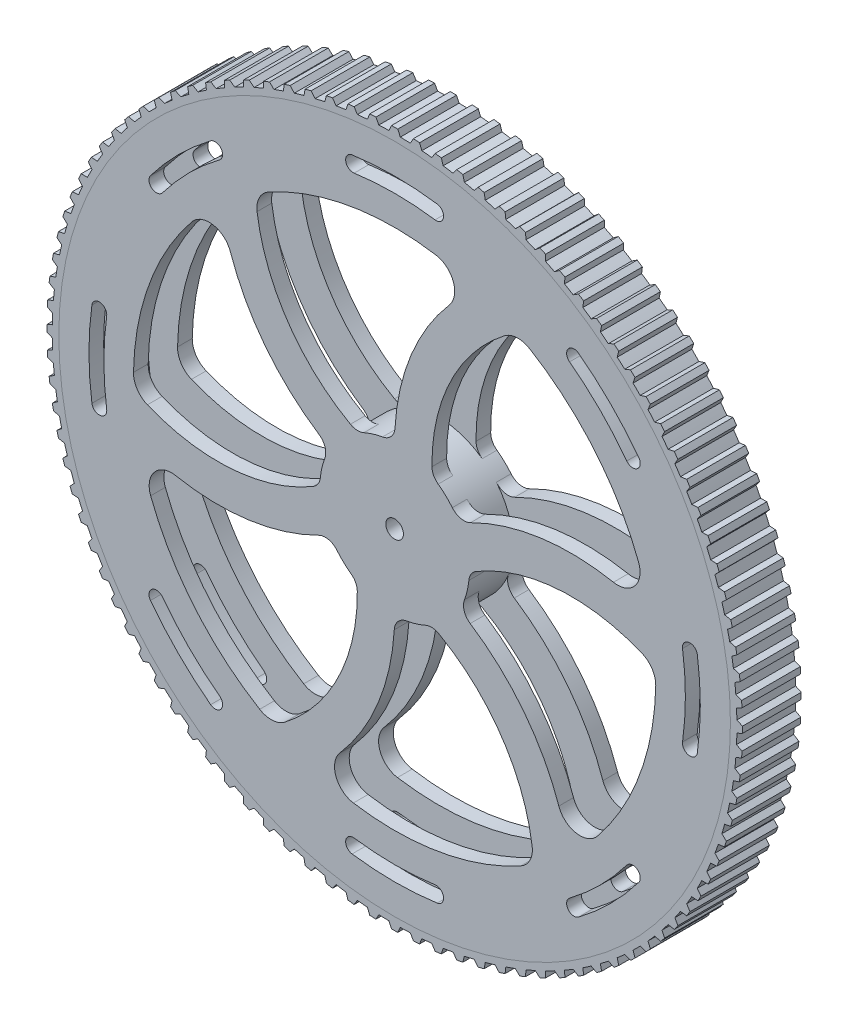
SolidWorks part; units mm, degrees
material "Acrylic (Medium-high impact)"
ref_plane "Front Plane" through (0, 0, 0) normal (0, 0, 1) x (1, 0, 0)
ref_plane "Top Plane" through (0, 0, 0) normal (0, 1, 0) x (1, 0, 0)
ref_plane "Right Plane" through (0, 0, 0) normal (1, 0, 0) x (0, 0, -1)
sketch "Sketch1" plane through (0, 0, 0) normal (0, 0, 1) x (1, 0, 0)
  circle A0 centre (0, 0) radius 114.3
  dimension "D1" = 228.6
extrude "Boss-Extrude1" add sketch "Sketch1" along normal mid plane 20
sketch "Sketch3" plane through (0, 0, 0) normal (0, 0, 1) x (1, 0, 0)
  line L0 (0, 0) -> (0, 114.3) construction
  circle A0 centre (0, 0) radius 114.3 construction
  circle A1 centre (0, 0) radius 88.9
  circle A2 centre (0, 0) radius 25.4
  arc A3 (27.9624, 84.3879) -> (0, 25.4) centre (76.2, 25.4) ccw
  arc A4 (41.5327, 78.6018) -> (12.7942, 21.9424) centre (76.2, 25.4) ccw
  arc A5 (87.0632, 17.9778) -> (21.997, 12.7) centre (60.097, -53.2911) ccw
  arc A6 (34.5993, 89.2422) -> (0.113, 21.2509) centre (76.2, 25.4) ccw construction
  arc A7 (88.8375, 3.3325) -> (25.3998, -0.1089) centre (60.097, -53.2911) ccw
  arc A8 (59.1009, -66.4101) -> (21.997, -12.7) centre (-16.103, -78.6911) ccw
  arc A9 (47.3048, -75.2693) -> (12.6056, -22.0513) centre (-16.103, -78.6911) ccw
  arc A10 (-27.9624, -84.3879) -> (0, -25.4) centre (-76.2, -25.4) ccw
  arc A11 (-41.5327, -78.6018) -> (-12.7942, -21.9424) centre (-76.2, -25.4) ccw
  arc A12 (-87.0632, -17.9778) -> (-21.997, -12.7) centre (-60.097, 53.2911) ccw
  arc A13 (-88.8375, -3.3325) -> (-25.3998, 0.1089) centre (-60.097, 53.2911) ccw
  arc A14 (-59.1009, 66.4101) -> (-21.997, 12.7) centre (16.103, 78.6911) ccw
  arc A15 (-47.3048, 75.2693) -> (-12.6056, 22.0513) centre (16.103, 78.6911) ccw
  point P50 (0, 0)
  dimension "D1" = 177.8
  dimension "D2" = 50.8
  dimension "D3" = 63.5
  dimension "D4" = 25.4
  dimension "D5" = 76.2
  dimension "D7" = 27.9624
  dimension "D8" = 84.3879
  dimension "D6" = 12.7
extrude "Cut-Extrude1" cut sketch "Sketch3" against normal mid plane 127 contours A14 A1 A13 A2 | A1 A15 A2 A3 | A5 A1 A4 A2 | A8 A1 A7 A2 | A10 A1 A9 A2 | A12 A1 A11 A2
fillet "Fillet1" radius 7.62 12 edges at (88.8375, 3.3325, 0) (59.1009, -66.4101, 0) (47.3048, -75.2693, 0) (-27.9624, -84.3879, 0) (-41.5327, -78.6018, 0) (-87.0632, -17.9778, 0) (87.0632, 17.9778, 0) (41.5327, 78.6018, 0) (27.9624, 84.3879, 0) (-47.3048, 75.2693, 0) (-59.1009, 66.4101, 0) (-88.8375, -3.3325, 0)
fillet "Fillet2" radius 5.08 12 edges at (-25.3998, 0.1089, 0) (-21.997, 12.7, 0) (0, 25.4, 0) (-12.6056, 22.0513, 0) (12.7942, 21.9424, 0) (21.997, 12.7, 0) (25.3998, -0.1089, 0) (21.997, -12.7, 0) (12.6056, -22.0513, 0) (0, -25.4, 0) (-12.7942, -21.9424, 0) (-21.997, -12.7, 0)
sketch "Sketch4" plane through (0, 0, 10) normal (0, 0, 1) x (1, 0, 0)
  circle A0 centre (0, 0) radius 3
  dimension "D1" = 6
extrude "Cut-Extrude2" cut sketch "Sketch4" against normal blind 127
sketch "Sketch5" plane through (0, 0, 0) normal (0, 0, 1) x (1, 0, 0)
  line L0 (0, 2.0217) -> (0, 118.4) construction
  line L1 (0, 2.0217) -> (0, 116.4837) construction
  line L2 (-1.0586, 118.3953) -> (-1.95, 116.4837)
  line L3 (1.0586, 118.3953) -> (1.95, 116.4837)
  line L4 (-1.95, 116.4837) -> (1.95, 116.4837) construction
  line L5 (8.4906, 118.0952) -> (9.2602, 116.1314)
  line L6 (6.3776, 118.2281) -> (5.3679, 116.3763)
  line L7 (15.8891, 117.329) -> (16.5339, 115.3208)
  line L8 (13.7886, 117.5944) -> (12.6647, 115.8096)
  line L9 (23.2249, 116.0998) -> (23.7423, 114.055)
  line L10 (21.1452, 116.4965) -> (19.9114, 114.7858)
  line L11 (30.4691, 114.4124) -> (30.8571, 112.3392)
  line L12 (28.4184, 114.9389) -> (27.0796, 113.3091)
  line L13 (37.5929, 112.2735) -> (37.85, 110.18)
  line L14 (35.5794, 112.9277) -> (34.1409, 111.3851)
  line L15 (44.5685, 109.6914) -> (44.6936, 107.5859)
  line L16 (42.5999, 110.4708) -> (41.0674, 109.0216)
  line L17 (51.3681, 106.6765) -> (51.3608, 104.5673)
  line L18 (49.4524, 107.578) -> (47.8319, 106.2279)
  line L19 (57.965, 103.2406) -> (57.8252, 101.136)
  line L20 (56.1097, 104.2606) -> (54.4076, 103.0148)
  line L21 (64.3332, 99.3972) -> (64.0615, 97.3056)
  line L22 (62.5455, 100.5317) -> (60.7686, 99.3953)
  line L23 (70.4474, 95.1615) -> (70.045, 93.0911)
  line L24 (68.7346, 96.406) -> (66.8898, 95.3835)
  line L25 (76.2837, 90.5503) -> (75.752, 88.5092)
  line L26 (74.6523, 91.8999) -> (72.747, 90.9952)
  line L27 (81.8188, 85.5818) -> (81.1601, 83.5781)
  line L28 (80.2754, 87.0311) -> (78.3171, 86.2478)
  line L29 (87.0311, 80.2754) -> (86.2478, 78.3171)
  line L30 (85.5818, 81.8188) -> (83.5781, 81.1601)
  line L31 (91.8999, 74.6523) -> (90.9952, 72.747)
  line L32 (90.5503, 76.2837) -> (88.5092, 75.752)
  line L33 (96.406, 68.7346) -> (95.3835, 66.8898)
  line L34 (95.1615, 70.4474) -> (93.0911, 70.045)
  line L35 (100.5317, 62.5455) -> (99.3953, 60.7686)
  line L36 (99.3972, 64.3332) -> (97.3056, 64.0615)
  line L37 (104.2606, 56.1097) -> (103.0148, 54.4076)
  line L38 (103.2406, 57.965) -> (101.136, 57.8252)
  line L39 (107.578, 49.4524) -> (106.2279, 47.8319)
  line L40 (106.6765, 51.3681) -> (104.5673, 51.3608)
  line L41 (110.4708, 42.5999) -> (109.0216, 41.0674)
  line L42 (109.6914, 44.5685) -> (107.5859, 44.6936)
  line L43 (112.9277, 35.5794) -> (111.3851, 34.1409)
  line L44 (112.2735, 37.5929) -> (110.18, 37.85)
  line L45 (114.9389, 28.4184) -> (113.3091, 27.0796)
  line L46 (114.4124, 30.4691) -> (112.3392, 30.8571)
  line L47 (116.4965, 21.1452) -> (114.7858, 19.9114)
  line L48 (116.0998, 23.2249) -> (114.055, 23.7423)
  line L49 (117.5944, 13.7886) -> (115.8096, 12.6647)
  line L50 (117.329, 15.8891) -> (115.3208, 16.5339)
  line L51 (118.2281, 6.3776) -> (116.3763, 5.3679)
  line L52 (118.0952, 8.4906) -> (116.1314, 9.2602)
  line L53 (118.3953, -1.0586) -> (116.4837, -1.95)
  line L54 (118.3953, 1.0586) -> (116.4837, 1.95)
  line L55 (118.0952, -8.4906) -> (116.1314, -9.2602)
  line L56 (118.2281, -6.3776) -> (116.3763, -5.3679)
  line L57 (117.329, -15.8891) -> (115.3208, -16.5339)
  line L58 (117.5944, -13.7886) -> (115.8096, -12.6647)
  line L59 (116.0998, -23.2249) -> (114.055, -23.7423)
  line L60 (116.4965, -21.1452) -> (114.7858, -19.9114)
  line L61 (114.4124, -30.4691) -> (112.3392, -30.8571)
  line L62 (114.9389, -28.4184) -> (113.3091, -27.0796)
  line L63 (112.2735, -37.5929) -> (110.18, -37.85)
  line L64 (112.9277, -35.5794) -> (111.3851, -34.1409)
  line L65 (109.6914, -44.5685) -> (107.5859, -44.6936)
  line L66 (110.4708, -42.5999) -> (109.0216, -41.0674)
  line L67 (106.6765, -51.3681) -> (104.5673, -51.3608)
  line L68 (107.578, -49.4524) -> (106.2279, -47.8319)
  line L69 (103.2406, -57.965) -> (101.136, -57.8252)
  line L70 (104.2606, -56.1097) -> (103.0148, -54.4076)
  line L71 (99.3972, -64.3332) -> (97.3056, -64.0615)
  line L72 (100.5317, -62.5455) -> (99.3953, -60.7686)
  line L73 (95.1615, -70.4474) -> (93.0911, -70.045)
  line L74 (96.406, -68.7346) -> (95.3835, -66.8898)
  line L75 (90.5503, -76.2837) -> (88.5092, -75.752)
  line L76 (91.8999, -74.6523) -> (90.9952, -72.747)
  line L77 (85.5818, -81.8188) -> (83.5781, -81.1601)
  line L78 (87.0311, -80.2754) -> (86.2478, -78.3171)
  line L79 (80.2754, -87.0311) -> (78.3171, -86.2478)
  line L80 (81.8188, -85.5818) -> (81.1601, -83.5781)
  line L81 (74.6523, -91.8999) -> (72.747, -90.9952)
  line L82 (76.2837, -90.5503) -> (75.752, -88.5092)
  line L83 (68.7346, -96.406) -> (66.8898, -95.3835)
  line L84 (70.4474, -95.1615) -> (70.045, -93.0911)
  line L85 (62.5455, -100.5317) -> (60.7686, -99.3953)
  line L86 (64.3332, -99.3972) -> (64.0615, -97.3056)
  line L87 (56.1097, -104.2606) -> (54.4076, -103.0148)
  line L88 (57.965, -103.2406) -> (57.8252, -101.136)
  line L89 (49.4524, -107.578) -> (47.8319, -106.2279)
  line L90 (51.3681, -106.6765) -> (51.3608, -104.5673)
  line L91 (42.5999, -110.4708) -> (41.0674, -109.0216)
  line L92 (44.5685, -109.6914) -> (44.6936, -107.5859)
  line L93 (35.5794, -112.9277) -> (34.1409, -111.3851)
  line L94 (37.5929, -112.2735) -> (37.85, -110.18)
  line L95 (28.4184, -114.9389) -> (27.0796, -113.3091)
  line L96 (30.4691, -114.4124) -> (30.8571, -112.3392)
  line L97 (21.1452, -116.4965) -> (19.9114, -114.7858)
  line L98 (23.2249, -116.0998) -> (23.7423, -114.055)
  line L99 (13.7886, -117.5944) -> (12.6647, -115.8096)
  line L100 (15.8891, -117.329) -> (16.5339, -115.3208)
  line L101 (6.3776, -118.2281) -> (5.3679, -116.3763)
  line L102 (8.4906, -118.0952) -> (9.2602, -116.1314)
  line L103 (-1.0586, -118.3953) -> (-1.95, -116.4837)
  line L104 (1.0586, -118.3953) -> (1.95, -116.4837)
  line L105 (-8.4906, -118.0952) -> (-9.2602, -116.1314)
  line L106 (-6.3776, -118.2281) -> (-5.3679, -116.3763)
  line L107 (-15.8891, -117.329) -> (-16.5339, -115.3208)
  line L108 (-13.7886, -117.5944) -> (-12.6647, -115.8096)
  line L109 (-23.2249, -116.0998) -> (-23.7423, -114.055)
  line L110 (-21.1452, -116.4965) -> (-19.9114, -114.7858)
  line L111 (-30.4691, -114.4124) -> (-30.8571, -112.3392)
  line L112 (-28.4184, -114.9389) -> (-27.0796, -113.3091)
  line L113 (-37.5929, -112.2735) -> (-37.85, -110.18)
  line L114 (-35.5794, -112.9277) -> (-34.1409, -111.3851)
  line L115 (-44.5685, -109.6914) -> (-44.6936, -107.5859)
  line L116 (-42.5999, -110.4708) -> (-41.0674, -109.0216)
  line L117 (-51.3681, -106.6765) -> (-51.3608, -104.5673)
  line L118 (-49.4524, -107.578) -> (-47.8319, -106.2279)
  line L119 (-57.965, -103.2406) -> (-57.8252, -101.136)
  line L120 (-56.1097, -104.2606) -> (-54.4076, -103.0148)
  line L121 (-64.3332, -99.3972) -> (-64.0615, -97.3056)
  line L122 (-62.5455, -100.5317) -> (-60.7686, -99.3953)
  line L123 (-70.4474, -95.1615) -> (-70.045, -93.0911)
  line L124 (-68.7346, -96.406) -> (-66.8898, -95.3835)
  line L125 (-76.2837, -90.5503) -> (-75.752, -88.5092)
  line L126 (-74.6523, -91.8999) -> (-72.747, -90.9952)
  line L127 (-81.8188, -85.5818) -> (-81.1601, -83.5781)
  line L128 (-80.2754, -87.0311) -> (-78.3171, -86.2478)
  line L129 (-87.0311, -80.2754) -> (-86.2478, -78.3171)
  line L130 (-85.5818, -81.8188) -> (-83.5781, -81.1601)
  line L131 (-91.8999, -74.6523) -> (-90.9952, -72.747)
  line L132 (-90.5503, -76.2837) -> (-88.5092, -75.752)
  line L133 (-96.406, -68.7346) -> (-95.3835, -66.8898)
  line L134 (-95.1615, -70.4474) -> (-93.0911, -70.045)
  line L135 (-100.5317, -62.5455) -> (-99.3953, -60.7686)
  line L136 (-99.3972, -64.3332) -> (-97.3056, -64.0615)
  line L137 (-104.2606, -56.1097) -> (-103.0148, -54.4076)
  line L138 (-103.2406, -57.965) -> (-101.136, -57.8252)
  line L139 (-107.578, -49.4524) -> (-106.2279, -47.8319)
  line L140 (-106.6765, -51.3681) -> (-104.5673, -51.3608)
  line L141 (-110.4708, -42.5999) -> (-109.0216, -41.0674)
  line L142 (-109.6914, -44.5685) -> (-107.5859, -44.6936)
  line L143 (-112.9277, -35.5794) -> (-111.3851, -34.1409)
  line L144 (-112.2735, -37.5929) -> (-110.18, -37.85)
  line L145 (-114.9389, -28.4184) -> (-113.3091, -27.0796)
  line L146 (-114.4124, -30.4691) -> (-112.3392, -30.8571)
  line L147 (-116.4965, -21.1452) -> (-114.7858, -19.9114)
  line L148 (-116.0998, -23.2249) -> (-114.055, -23.7423)
  line L149 (-117.5944, -13.7886) -> (-115.8096, -12.6647)
  line L150 (-117.329, -15.8891) -> (-115.3208, -16.5339)
  line L151 (-118.2281, -6.3776) -> (-116.3763, -5.3679)
  line L152 (-118.0952, -8.4906) -> (-116.1314, -9.2602)
  line L153 (-118.3953, 1.0586) -> (-116.4837, 1.95)
  line L154 (-118.3953, -1.0586) -> (-116.4837, -1.95)
  line L155 (-118.0952, 8.4906) -> (-116.1314, 9.2602)
  line L156 (-118.2281, 6.3776) -> (-116.3763, 5.3679)
  line L157 (-117.329, 15.8891) -> (-115.3208, 16.5339)
  line L158 (-117.5944, 13.7886) -> (-115.8096, 12.6647)
  line L159 (-116.0998, 23.2249) -> (-114.055, 23.7423)
  line L160 (-116.4965, 21.1452) -> (-114.7858, 19.9114)
  line L161 (-114.4124, 30.4691) -> (-112.3392, 30.8571)
  line L162 (-114.9389, 28.4184) -> (-113.3091, 27.0796)
  line L163 (-112.2735, 37.5929) -> (-110.18, 37.85)
  line L164 (-112.9277, 35.5794) -> (-111.3851, 34.1409)
  line L165 (-109.6914, 44.5685) -> (-107.5859, 44.6936)
  line L166 (-110.4708, 42.5999) -> (-109.0216, 41.0674)
  line L167 (-106.6765, 51.3681) -> (-104.5673, 51.3608)
  line L168 (-107.578, 49.4524) -> (-106.2279, 47.8319)
  line L169 (-103.2406, 57.965) -> (-101.136, 57.8252)
  line L170 (-104.2606, 56.1097) -> (-103.0148, 54.4076)
  line L171 (-99.3972, 64.3332) -> (-97.3056, 64.0615)
  line L172 (-100.5317, 62.5455) -> (-99.3953, 60.7686)
  line L173 (-95.1615, 70.4474) -> (-93.0911, 70.045)
  line L174 (-96.406, 68.7346) -> (-95.3835, 66.8898)
  line L175 (-90.5503, 76.2837) -> (-88.5092, 75.752)
  line L176 (-91.8999, 74.6523) -> (-90.9952, 72.747)
  line L177 (-85.5818, 81.8188) -> (-83.5781, 81.1601)
  line L178 (-87.0311, 80.2754) -> (-86.2478, 78.3171)
  line L179 (-80.2754, 87.0311) -> (-78.3171, 86.2478)
  line L180 (-81.8188, 85.5818) -> (-81.1601, 83.5781)
  line L181 (-74.6523, 91.8999) -> (-72.747, 90.9952)
  line L182 (-76.2837, 90.5503) -> (-75.752, 88.5092)
  line L183 (-68.7346, 96.406) -> (-66.8898, 95.3835)
  line L184 (-70.4474, 95.1615) -> (-70.045, 93.0911)
  line L185 (-62.5455, 100.5317) -> (-60.7686, 99.3953)
  line L186 (-64.3332, 99.3972) -> (-64.0615, 97.3056)
  line L187 (-56.1097, 104.2606) -> (-54.4076, 103.0148)
  line L188 (-57.965, 103.2406) -> (-57.8252, 101.136)
  line L189 (-49.4524, 107.578) -> (-47.8319, 106.2279)
  line L190 (-51.3681, 106.6765) -> (-51.3608, 104.5673)
  line L191 (-42.5999, 110.4708) -> (-41.0674, 109.0216)
  line L192 (-44.5685, 109.6914) -> (-44.6936, 107.5859)
  line L193 (-35.5794, 112.9277) -> (-34.1409, 111.3851)
  line L194 (-37.5929, 112.2735) -> (-37.85, 110.18)
  line L195 (-28.4184, 114.9389) -> (-27.0796, 113.3091)
  line L196 (-30.4691, 114.4124) -> (-30.8571, 112.3392)
  line L197 (-21.1452, 116.4965) -> (-19.9114, 114.7858)
  line L198 (-23.2249, 116.0998) -> (-23.7423, 114.055)
  line L199 (-13.7886, 117.5944) -> (-12.6647, 115.8096)
  line L200 (-15.8891, 117.329) -> (-16.5339, 115.3208)
  line L201 (-6.3776, 118.2281) -> (-5.3679, 116.3763)
  line L202 (-8.4906, 118.0952) -> (-9.2602, 116.1314)
  circle A0 centre (0, 0) radius 114.3 construction
  circle A1 centre (0, 0) radius 114.3
  arc A2 (1.0586, 118.3953) -> (-1.0586, 118.3953) centre (0, 0) ccw
  arc A3 (5.3679, 116.3763) -> (1.95, 116.4837) centre (0, 0) ccw
  arc A4 (8.4906, 118.0952) -> (6.3776, 118.2281) centre (0, 0) ccw
  circle A5 centre (0, 0) radius 118.4 construction
  arc A6 (15.8891, 117.329) -> (13.7886, 117.5944) centre (0, 0) ccw
  arc A7 (23.2249, 116.0998) -> (21.1452, 116.4965) centre (0, 0) ccw
  arc A8 (30.4691, 114.4124) -> (28.4184, 114.9389) centre (0, 0) ccw
  arc A9 (37.5929, 112.2735) -> (35.5794, 112.9277) centre (0, 0) ccw
  arc A10 (44.5685, 109.6914) -> (42.5999, 110.4708) centre (0, 0) ccw
  arc A11 (51.3681, 106.6765) -> (49.4524, 107.578) centre (0, 0) ccw
  arc A12 (57.965, 103.2406) -> (56.1097, 104.2606) centre (0, 0) ccw
  arc A13 (64.3332, 99.3972) -> (62.5455, 100.5317) centre (0, 0) ccw
  arc A14 (70.4474, 95.1615) -> (68.7346, 96.406) centre (0, 0) ccw
  arc A15 (76.2837, 90.5503) -> (74.6523, 91.8999) centre (0, 0) ccw
  arc A16 (81.8188, 85.5818) -> (80.2754, 87.0311) centre (0, 0) ccw
  arc A17 (87.0311, 80.2754) -> (85.5818, 81.8188) centre (0, 0) ccw
  arc A18 (91.8999, 74.6523) -> (90.5503, 76.2837) centre (0, 0) ccw
  arc A19 (96.406, 68.7346) -> (95.1615, 70.4474) centre (0, 0) ccw
  arc A20 (100.5317, 62.5455) -> (99.3972, 64.3332) centre (0, 0) ccw
  arc A21 (104.2606, 56.1097) -> (103.2406, 57.965) centre (0, 0) ccw
  arc A22 (107.578, 49.4524) -> (106.6765, 51.3681) centre (0, 0) ccw
  arc A23 (110.4708, 42.5999) -> (109.6914, 44.5685) centre (0, 0) ccw
  arc A24 (112.9277, 35.5794) -> (112.2735, 37.5929) centre (0, 0) ccw
  arc A25 (114.9389, 28.4184) -> (114.4124, 30.4691) centre (0, 0) ccw
  arc A26 (116.4965, 21.1452) -> (116.0998, 23.2249) centre (0, 0) ccw
  arc A27 (117.5944, 13.7886) -> (117.329, 15.8891) centre (0, 0) ccw
  arc A28 (118.2281, 6.3776) -> (118.0952, 8.4906) centre (0, 0) ccw
  arc A29 (118.3953, -1.0586) -> (118.3953, 1.0586) centre (0, 0) ccw
  arc A30 (118.0952, -8.4906) -> (118.2281, -6.3776) centre (0, 0) ccw
  arc A31 (117.329, -15.8891) -> (117.5944, -13.7886) centre (0, 0) ccw
  arc A32 (116.0998, -23.2249) -> (116.4965, -21.1452) centre (0, 0) ccw
  arc A33 (114.4124, -30.4691) -> (114.9389, -28.4184) centre (0, 0) ccw
  arc A34 (112.2735, -37.5929) -> (112.9277, -35.5794) centre (0, 0) ccw
  arc A35 (109.6914, -44.5685) -> (110.4708, -42.5999) centre (0, 0) ccw
  arc A36 (106.6765, -51.3681) -> (107.578, -49.4524) centre (0, 0) ccw
  arc A37 (103.2406, -57.965) -> (104.2606, -56.1097) centre (0, 0) ccw
  arc A38 (99.3972, -64.3332) -> (100.5317, -62.5455) centre (0, 0) ccw
  arc A39 (95.1615, -70.4474) -> (96.406, -68.7346) centre (0, 0) ccw
  arc A40 (90.5503, -76.2837) -> (91.8999, -74.6523) centre (0, 0) ccw
  arc A41 (85.5818, -81.8188) -> (87.0311, -80.2754) centre (0, 0) ccw
  arc A42 (80.2754, -87.0311) -> (81.8188, -85.5818) centre (0, 0) ccw
  arc A43 (74.6523, -91.8999) -> (76.2837, -90.5503) centre (0, 0) ccw
  arc A44 (68.7346, -96.406) -> (70.4474, -95.1615) centre (0, 0) ccw
  arc A45 (62.5455, -100.5317) -> (64.3332, -99.3972) centre (0, 0) ccw
  arc A46 (56.1097, -104.2606) -> (57.965, -103.2406) centre (0, 0) ccw
  arc A47 (49.4524, -107.578) -> (51.3681, -106.6765) centre (0, 0) ccw
  arc A48 (42.5999, -110.4708) -> (44.5685, -109.6914) centre (0, 0) ccw
  arc A49 (35.5794, -112.9277) -> (37.5929, -112.2735) centre (0, 0) ccw
  arc A50 (28.4184, -114.9389) -> (30.4691, -114.4124) centre (0, 0) ccw
  arc A51 (21.1452, -116.4965) -> (23.2249, -116.0998) centre (0, 0) ccw
  arc A52 (13.7886, -117.5944) -> (15.8891, -117.329) centre (0, 0) ccw
  arc A53 (6.3776, -118.2281) -> (8.4906, -118.0952) centre (0, 0) ccw
  arc A54 (-1.0586, -118.3953) -> (1.0586, -118.3953) centre (0, 0) ccw
  arc A55 (-8.4906, -118.0952) -> (-6.3776, -118.2281) centre (0, 0) ccw
  arc A56 (-15.8891, -117.329) -> (-13.7886, -117.5944) centre (0, 0) ccw
  arc A57 (-23.2249, -116.0998) -> (-21.1452, -116.4965) centre (0, 0) ccw
  arc A58 (-30.4691, -114.4124) -> (-28.4184, -114.9389) centre (0, 0) ccw
  arc A59 (-37.5929, -112.2735) -> (-35.5794, -112.9277) centre (0, 0) ccw
  arc A60 (-44.5685, -109.6914) -> (-42.5999, -110.4708) centre (0, 0) ccw
  arc A61 (-51.3681, -106.6765) -> (-49.4524, -107.578) centre (0, 0) ccw
  arc A62 (-57.965, -103.2406) -> (-56.1097, -104.2606) centre (0, 0) ccw
  arc A63 (-64.3332, -99.3972) -> (-62.5455, -100.5317) centre (0, 0) ccw
  arc A64 (-70.4474, -95.1615) -> (-68.7346, -96.406) centre (0, 0) ccw
  arc A65 (-76.2837, -90.5503) -> (-74.6523, -91.8999) centre (0, 0) ccw
  arc A66 (-81.8188, -85.5818) -> (-80.2754, -87.0311) centre (0, 0) ccw
  arc A67 (-87.0311, -80.2754) -> (-85.5818, -81.8188) centre (0, 0) ccw
  arc A68 (-91.8999, -74.6523) -> (-90.5503, -76.2837) centre (0, 0) ccw
  arc A69 (-96.406, -68.7346) -> (-95.1615, -70.4474) centre (0, 0) ccw
  arc A70 (-100.5317, -62.5455) -> (-99.3972, -64.3332) centre (0, 0) ccw
  arc A71 (-104.2606, -56.1097) -> (-103.2406, -57.965) centre (0, 0) ccw
  arc A72 (-107.578, -49.4524) -> (-106.6765, -51.3681) centre (0, 0) ccw
  arc A73 (-110.4708, -42.5999) -> (-109.6914, -44.5685) centre (0, 0) ccw
  arc A74 (-112.9277, -35.5794) -> (-112.2735, -37.5929) centre (0, 0) ccw
  arc A75 (-114.9389, -28.4184) -> (-114.4124, -30.4691) centre (0, 0) ccw
  arc A76 (-116.4965, -21.1452) -> (-116.0998, -23.2249) centre (0, 0) ccw
  arc A77 (-117.5944, -13.7886) -> (-117.329, -15.8891) centre (0, 0) ccw
  arc A78 (-118.2281, -6.3776) -> (-118.0952, -8.4906) centre (0, 0) ccw
  arc A79 (-118.3953, 1.0586) -> (-118.3953, -1.0586) centre (0, 0) ccw
  arc A80 (-118.0952, 8.4906) -> (-118.2281, 6.3776) centre (0, 0) ccw
  arc A81 (-117.329, 15.8891) -> (-117.5944, 13.7886) centre (0, 0) ccw
  arc A82 (-116.0998, 23.2249) -> (-116.4965, 21.1452) centre (0, 0) ccw
  arc A83 (-114.4124, 30.4691) -> (-114.9389, 28.4184) centre (0, 0) ccw
  arc A84 (-112.2735, 37.5929) -> (-112.9277, 35.5794) centre (0, 0) ccw
  arc A85 (-109.6914, 44.5685) -> (-110.4708, 42.5999) centre (0, 0) ccw
  arc A86 (-106.6765, 51.3681) -> (-107.578, 49.4524) centre (0, 0) ccw
  arc A87 (-103.2406, 57.965) -> (-104.2606, 56.1097) centre (0, 0) ccw
  arc A88 (-99.3972, 64.3332) -> (-100.5317, 62.5455) centre (0, 0) ccw
  arc A89 (-95.1615, 70.4474) -> (-96.406, 68.7346) centre (0, 0) ccw
  arc A90 (-90.5503, 76.2837) -> (-91.8999, 74.6523) centre (0, 0) ccw
  arc A91 (-85.5818, 81.8188) -> (-87.0311, 80.2754) centre (0, 0) ccw
  arc A92 (-80.2754, 87.0311) -> (-81.8188, 85.5818) centre (0, 0) ccw
  arc A93 (-74.6523, 91.8999) -> (-76.2837, 90.5503) centre (0, 0) ccw
  arc A94 (-68.7346, 96.406) -> (-70.4474, 95.1615) centre (0, 0) ccw
  arc A95 (-62.5455, 100.5317) -> (-64.3332, 99.3972) centre (0, 0) ccw
  arc A96 (-56.1097, 104.2606) -> (-57.965, 103.2406) centre (0, 0) ccw
  arc A97 (-49.4524, 107.578) -> (-51.3681, 106.6765) centre (0, 0) ccw
  arc A98 (-42.5999, 110.4708) -> (-44.5685, 109.6914) centre (0, 0) ccw
  arc A99 (-35.5794, 112.9277) -> (-37.5929, 112.2735) centre (0, 0) ccw
  arc A100 (-28.4184, 114.9389) -> (-30.4691, 114.4124) centre (0, 0) ccw
  arc A101 (-21.1452, 116.4965) -> (-23.2249, 116.0998) centre (0, 0) ccw
  arc A102 (-13.7886, 117.5944) -> (-15.8891, 117.329) centre (0, 0) ccw
  arc A103 (-6.3776, 118.2281) -> (-8.4906, 118.0952) centre (0, 0) ccw
  arc A104 (12.6647, 115.8096) -> (9.2602, 116.1314) centre (0, 0) ccw
  circle A105 centre (0, 0) radius 116.5 construction
  arc A106 (19.9114, 114.7858) -> (16.5339, 115.3208) centre (0, 0) ccw
  arc A107 (27.0796, 113.3091) -> (23.7423, 114.055) centre (0, 0) ccw
  arc A108 (34.1409, 111.3851) -> (30.8571, 112.3392) centre (0, 0) ccw
  arc A109 (41.0674, 109.0216) -> (37.85, 110.18) centre (0, 0) ccw
  arc A110 (47.8319, 106.2279) -> (44.6936, 107.5859) centre (0, 0) ccw
  arc A111 (54.4076, 103.0148) -> (51.3608, 104.5673) centre (0, 0) ccw
  arc A112 (60.7686, 99.3953) -> (57.8252, 101.136) centre (0, 0) ccw
  arc A113 (66.8898, 95.3835) -> (64.0615, 97.3056) centre (0, 0) ccw
  arc A114 (72.747, 90.9952) -> (70.045, 93.0911) centre (0, 0) ccw
  arc A115 (83.5781, 81.1601) -> (81.1601, 83.5781) centre (0, 0) ccw
  arc A116 (88.5092, 75.752) -> (86.2478, 78.3171) centre (0, 0) ccw
  arc A117 (93.0911, 70.045) -> (90.9952, 72.747) centre (0, 0) ccw
  arc A118 (97.3056, 64.0615) -> (95.3835, 66.8898) centre (0, 0) ccw
  arc A119 (101.136, 57.8252) -> (99.3953, 60.7686) centre (0, 0) ccw
  arc A120 (104.5673, 51.3608) -> (103.0148, 54.4076) centre (0, 0) ccw
  arc A121 (107.5859, 44.6936) -> (106.2279, 47.8319) centre (0, 0) ccw
  arc A122 (110.18, 37.85) -> (109.0216, 41.0674) centre (0, 0) ccw
  arc A123 (112.3392, 30.8571) -> (111.3851, 34.1409) centre (0, 0) ccw
  arc A124 (114.055, 23.7423) -> (113.3091, 27.0796) centre (0, 0) ccw
  arc A125 (115.3208, 16.5339) -> (114.7858, 19.9114) centre (0, 0) ccw
  arc A126 (116.1314, 9.2602) -> (115.8096, 12.6647) centre (0, 0) ccw
  arc A127 (116.4837, 1.95) -> (116.3763, 5.3679) centre (0, 0) ccw
  arc A128 (116.3763, -5.3679) -> (116.4837, -1.95) centre (0, 0) ccw
  arc A129 (115.8096, -12.6647) -> (116.1314, -9.2602) centre (0, 0) ccw
  arc A130 (114.7858, -19.9114) -> (115.3208, -16.5339) centre (0, 0) ccw
  arc A131 (113.3091, -27.0796) -> (114.055, -23.7423) centre (0, 0) ccw
  arc A132 (111.3851, -34.1409) -> (112.3392, -30.8571) centre (0, 0) ccw
  arc A133 (109.0216, -41.0674) -> (110.18, -37.85) centre (0, 0) ccw
  arc A134 (106.2279, -47.8319) -> (107.5859, -44.6936) centre (0, 0) ccw
  arc A135 (103.0148, -54.4076) -> (104.5673, -51.3608) centre (0, 0) ccw
  arc A136 (99.3953, -60.7686) -> (101.136, -57.8252) centre (0, 0) ccw
  arc A137 (95.3835, -66.8898) -> (97.3056, -64.0615) centre (0, 0) ccw
  arc A138 (90.9952, -72.747) -> (93.0911, -70.045) centre (0, 0) ccw
  arc A139 (86.2478, -78.3171) -> (88.5092, -75.752) centre (0, 0) ccw
  arc A140 (81.1601, -83.5781) -> (83.5781, -81.1601) centre (0, 0) ccw
  arc A141 (75.752, -88.5092) -> (78.3171, -86.2478) centre (0, 0) ccw
  arc A142 (70.045, -93.0911) -> (72.747, -90.9952) centre (0, 0) ccw
  arc A143 (64.0615, -97.3056) -> (66.8898, -95.3835) centre (0, 0) ccw
  arc A144 (57.8252, -101.136) -> (60.7686, -99.3953) centre (0, 0) ccw
  arc A145 (51.3608, -104.5673) -> (54.4076, -103.0148) centre (0, 0) ccw
  arc A146 (44.6936, -107.5859) -> (47.8319, -106.2279) centre (0, 0) ccw
  arc A147 (37.85, -110.18) -> (41.0674, -109.0216) centre (0, 0) ccw
  arc A148 (30.8571, -112.3392) -> (34.1409, -111.3851) centre (0, 0) ccw
  arc A149 (23.7423, -114.055) -> (27.0796, -113.3091) centre (0, 0) ccw
  arc A150 (16.5339, -115.3208) -> (19.9114, -114.7858) centre (0, 0) ccw
  arc A151 (9.2602, -116.1314) -> (12.6647, -115.8096) centre (0, 0) ccw
  arc A152 (1.95, -116.4837) -> (5.3679, -116.3763) centre (0, 0) ccw
  arc A153 (-5.3679, -116.3763) -> (-1.95, -116.4837) centre (0, 0) ccw
  arc A154 (-12.6647, -115.8096) -> (-9.2602, -116.1314) centre (0, 0) ccw
  arc A155 (-19.9114, -114.7858) -> (-16.5339, -115.3208) centre (0, 0) ccw
  arc A156 (-27.0796, -113.3091) -> (-23.7423, -114.055) centre (0, 0) ccw
  arc A157 (-34.1409, -111.3851) -> (-30.8571, -112.3392) centre (0, 0) ccw
  arc A158 (-41.0674, -109.0216) -> (-37.85, -110.18) centre (0, 0) ccw
  arc A159 (-47.8319, -106.2279) -> (-44.6936, -107.5859) centre (0, 0) ccw
  arc A160 (-54.4076, -103.0148) -> (-51.3608, -104.5673) centre (0, 0) ccw
  arc A161 (-60.7686, -99.3953) -> (-57.8252, -101.136) centre (0, 0) ccw
  arc A162 (-66.8898, -95.3835) -> (-64.0615, -97.3056) centre (0, 0) ccw
  arc A163 (-72.747, -90.9952) -> (-70.045, -93.0911) centre (0, 0) ccw
  arc A164 (-78.3171, -86.2478) -> (-75.752, -88.5092) centre (0, 0) ccw
  arc A165 (-83.5781, -81.1601) -> (-81.1601, -83.5781) centre (0, 0) ccw
  arc A166 (-88.5092, -75.752) -> (-86.2478, -78.3171) centre (0, 0) ccw
  arc A167 (-93.0911, -70.045) -> (-90.9952, -72.747) centre (0, 0) ccw
  arc A168 (-107.5859, -44.6936) -> (-106.2279, -47.8319) centre (0, 0) ccw
  arc A169 (-110.18, -37.85) -> (-109.0216, -41.0674) centre (0, 0) ccw
  arc A170 (-112.3392, -30.8571) -> (-111.3851, -34.1409) centre (0, 0) ccw
  arc A171 (-114.055, -23.7423) -> (-113.3091, -27.0796) centre (0, 0) ccw
  arc A172 (-115.3208, -16.5339) -> (-114.7858, -19.9114) centre (0, 0) ccw
  arc A173 (-116.1314, -9.2602) -> (-115.8096, -12.6647) centre (0, 0) ccw
  arc A174 (-116.4837, -1.95) -> (-116.3763, -5.3679) centre (0, 0) ccw
  arc A175 (-116.3763, 5.3679) -> (-116.4837, 1.95) centre (0, 0) ccw
  arc A176 (-115.8096, 12.6647) -> (-116.1314, 9.2602) centre (0, 0) ccw
  arc A177 (-114.7858, 19.9114) -> (-115.3208, 16.5339) centre (0, 0) ccw
  arc A178 (-113.3091, 27.0796) -> (-114.055, 23.7423) centre (0, 0) ccw
  arc A179 (-111.3851, 34.1409) -> (-112.3392, 30.8571) centre (0, 0) ccw
  arc A180 (-109.0216, 41.0674) -> (-110.18, 37.85) centre (0, 0) ccw
  arc A181 (-106.2279, 47.8319) -> (-107.5859, 44.6936) centre (0, 0) ccw
  arc A182 (-103.0148, 54.4076) -> (-104.5673, 51.3608) centre (0, 0) ccw
  arc A183 (-99.3953, 60.7686) -> (-101.136, 57.8252) centre (0, 0) ccw
  arc A184 (-95.3835, 66.8898) -> (-97.3056, 64.0615) centre (0, 0) ccw
  arc A185 (-90.9952, 72.747) -> (-93.0911, 70.045) centre (0, 0) ccw
  arc A186 (-86.2478, 78.3171) -> (-88.5092, 75.752) centre (0, 0) ccw
  arc A187 (-81.1601, 83.5781) -> (-83.5781, 81.1601) centre (0, 0) ccw
  arc A188 (-75.752, 88.5092) -> (-78.3171, 86.2478) centre (0, 0) ccw
  arc A189 (-70.045, 93.0911) -> (-72.747, 90.9952) centre (0, 0) ccw
  arc A190 (-64.0615, 97.3056) -> (-66.8898, 95.3835) centre (0, 0) ccw
  arc A191 (-57.8252, 101.136) -> (-60.7686, 99.3953) centre (0, 0) ccw
  arc A192 (-51.3608, 104.5673) -> (-54.4076, 103.0148) centre (0, 0) ccw
  arc A193 (-44.6936, 107.5859) -> (-47.8319, 106.2279) centre (0, 0) ccw
  arc A194 (-37.85, 110.18) -> (-41.0674, 109.0216) centre (0, 0) ccw
  arc A195 (-30.8571, 112.3392) -> (-34.1409, 111.3851) centre (0, 0) ccw
  arc A196 (-23.7423, 114.055) -> (-27.0796, 113.3091) centre (0, 0) ccw
  arc A197 (-16.5339, 115.3208) -> (-19.9114, 114.7858) centre (0, 0) ccw
  arc A198 (-9.2602, 116.1314) -> (-12.6647, 115.8096) centre (0, 0) ccw
  arc A199 (-1.95, 116.4837) -> (-5.3679, 116.3763) centre (0, 0) ccw
  arc A200 (78.3171, 86.2478) -> (75.752, 88.5092) centre (0, 0) ccw
  arc A201 (-97.3056, -64.0615) -> (-95.3835, -66.8898) centre (0, 0) ccw
  arc A202 (-101.136, -57.8252) -> (-99.3953, -60.7686) centre (0, 0) ccw
  arc A203 (-104.5673, -51.3608) -> (-103.0148, -54.4076) centre (0, 0) ccw
  point P6 (103.8, 0)
  point P10 (105.7, 0)
  point P12 (0, 118.4)
  point P415 (0, 0)
  dimension "D2" = 1.9
  dimension "D1" = 4.1
  dimension "D3" = 65
  dimension "D4" = 65
  dimension "D5" = 3.9
  dimension "D6" = 100
extrude "Boss-Extrude2" add sketch "Sketch5" along normal mid plane 20 separate body contours L2 A199 L201 A103 L202 A198 L199 A102 L200 A197 L197 A101 L198 A196 L195 A100 L196 A195 L193 A99 L194 A194 L191 A98 L192 A193 L189 A97 L190 A192 L187 A96 L188 A191 L185 A95 L186 A190 L183 A94 L184 A189 L181 A93 L182 A188 L179 A92 L180 A187 L177
sketch "Sketch6" plane through (0, 0, 10) normal (0, 0, 1) x (1, 0, 0)
  line L0 (0, 0) -> (0, 101.5049) construction
  line L1 (0, 0) -> (-14.1268, 100.517) construction
  line L2 (14.1268, 100.517) -> (0, 0) construction
  circle A0 centre (0, 0) radius 101.5049 construction
  arc A1 (-14.1268, 100.517) -> (14.1268, 100.517) centre (0, 0) cw construction
  arc A2 (14.4802, 103.0323) -> (-14.4802, 103.0323) centre (0, 0) ccw
  arc A3 (13.7733, 98.0018) -> (-13.7733, 98.0018) centre (0, 0) ccw
  arc A4 (13.7733, 98.0018) -> (14.4802, 103.0323) centre (14.1268, 100.517) ccw
  arc A5 (-14.4802, 103.0323) -> (-13.7733, 98.0018) centre (-14.1268, 100.517) ccw
  arc A6 (61.0872, 81.0654) -> (81.0654, 61.0872) centre (0, 0) cw construction
  arc A7 (83.0939, 62.6158) -> (62.6158, 83.0939) centre (0, 0) ccw
  arc A8 (79.0369, 59.5586) -> (59.5586, 79.0369) centre (0, 0) ccw
  arc A9 (79.0369, 59.5586) -> (83.0939, 62.6158) centre (81.0654, 61.0872) ccw
  arc A10 (62.6158, 83.0939) -> (59.5586, 79.0369) centre (61.0872, 81.0654) ccw
  arc A11 (100.517, 14.1268) -> (100.517, -14.1268) centre (0, 0) cw construction
  arc A12 (103.0323, -14.4802) -> (103.0323, 14.4802) centre (0, 0) ccw
  arc A13 (98.0018, -13.7733) -> (98.0018, 13.7733) centre (0, 0) ccw
  arc A14 (98.0018, -13.7733) -> (103.0323, -14.4802) centre (100.517, -14.1268) ccw
  arc A15 (103.0323, 14.4802) -> (98.0018, 13.7733) centre (100.517, 14.1268) ccw
  arc A16 (81.0654, -61.0872) -> (61.0872, -81.0654) centre (0, 0) cw construction
  arc A17 (62.6158, -83.0939) -> (83.0939, -62.6158) centre (0, 0) ccw
  arc A18 (59.5586, -79.0369) -> (79.0369, -59.5586) centre (0, 0) ccw
  arc A19 (59.5586, -79.0369) -> (62.6158, -83.0939) centre (61.0872, -81.0654) ccw
  arc A20 (83.0939, -62.6158) -> (79.0369, -59.5586) centre (81.0654, -61.0872) ccw
  arc A21 (14.1268, -100.517) -> (-14.1268, -100.517) centre (0, 0) cw construction
  arc A22 (-14.4802, -103.0323) -> (14.4802, -103.0323) centre (0, 0) ccw
  arc A23 (-13.7733, -98.0018) -> (13.7733, -98.0018) centre (0, 0) ccw
  arc A24 (-13.7733, -98.0018) -> (-14.4802, -103.0323) centre (-14.1268, -100.517) ccw
  arc A25 (14.4802, -103.0323) -> (13.7733, -98.0018) centre (14.1268, -100.517) ccw
  arc A26 (-61.0872, -81.0654) -> (-81.0654, -61.0872) centre (0, 0) cw construction
  arc A27 (-83.0939, -62.6158) -> (-62.6158, -83.0939) centre (0, 0) ccw
  arc A28 (-79.0369, -59.5586) -> (-59.5586, -79.0369) centre (0, 0) ccw
  arc A29 (-79.0369, -59.5586) -> (-83.0939, -62.6158) centre (-81.0654, -61.0872) ccw
  arc A30 (-62.6158, -83.0939) -> (-59.5586, -79.0369) centre (-61.0872, -81.0654) ccw
  arc A31 (-100.517, -14.1268) -> (-100.517, 14.1268) centre (0, 0) cw construction
  arc A32 (-103.0323, 14.4802) -> (-103.0323, -14.4802) centre (0, 0) ccw
  arc A33 (-98.0018, 13.7733) -> (-98.0018, -13.7733) centre (0, 0) ccw
  arc A34 (-98.0018, 13.7733) -> (-103.0323, 14.4802) centre (-100.517, 14.1268) ccw
  arc A35 (-103.0323, -14.4802) -> (-98.0018, -13.7733) centre (-100.517, -14.1268) ccw
  arc A36 (-81.0654, 61.0872) -> (-61.0872, 81.0654) centre (0, 0) cw construction
  arc A37 (-62.6158, 83.0939) -> (-83.0939, 62.6158) centre (0, 0) ccw
  arc A38 (-59.5586, 79.0369) -> (-79.0369, 59.5586) centre (0, 0) ccw
  arc A39 (-59.5586, 79.0369) -> (-62.6158, 83.0939) centre (-61.0872, 81.0654) ccw
  arc A40 (-83.0939, 62.6158) -> (-79.0369, 59.5586) centre (-81.0654, 61.0872) ccw
  point P7 (0, 101.5049)
  point P19 (71.7748, 71.7748)
  point P26 (101.5049, 0)
  point P33 (71.7748, -71.7748)
  point P40 (0, -101.5049)
  point P47 (-71.7748, -71.7748)
  point P54 (-101.5049, 0)
  point P61 (-71.7748, 71.7748)
  point P66 (0, 0)
  dimension "D2" = 2.54
  dimension "D1" = 101.5049
  dimension "D3" = 8
  dimension "D4" = 8
extrude "Cut-Extrude5" cut sketch "Sketch6" against normal through all
sketch "Sketch7" plane through (0, 0, 0) normal (1, 0, 0) x (0, 0, -1)
  line L0 (-10, 114.3) -> (10, 114.3) construction
  line L1 (-5, 114.3) -> (5, 114.3)
  line L2 (-5, 114.3) -> (-5, 25.4)
  line L3 (-5, 25.4) -> (5, 25.4)
  line L4 (5, 114.3) -> (5, 25.4)
  line L5 (10, -114.3) -> (10, 114.3) construction
  line L6 (10, 114.3) -> (-10, 114.3) construction
  line L7 (0, 0) -> (106.9262, 0) construction
  dimension "D1" = 5
  dimension "D2" = 5
  dimension "D3" = 25.4
revolve "Cut-Revolve1" cut sketch "Sketch7" angle 360 about L7
equation "\"2cn\"=0.0787402"
